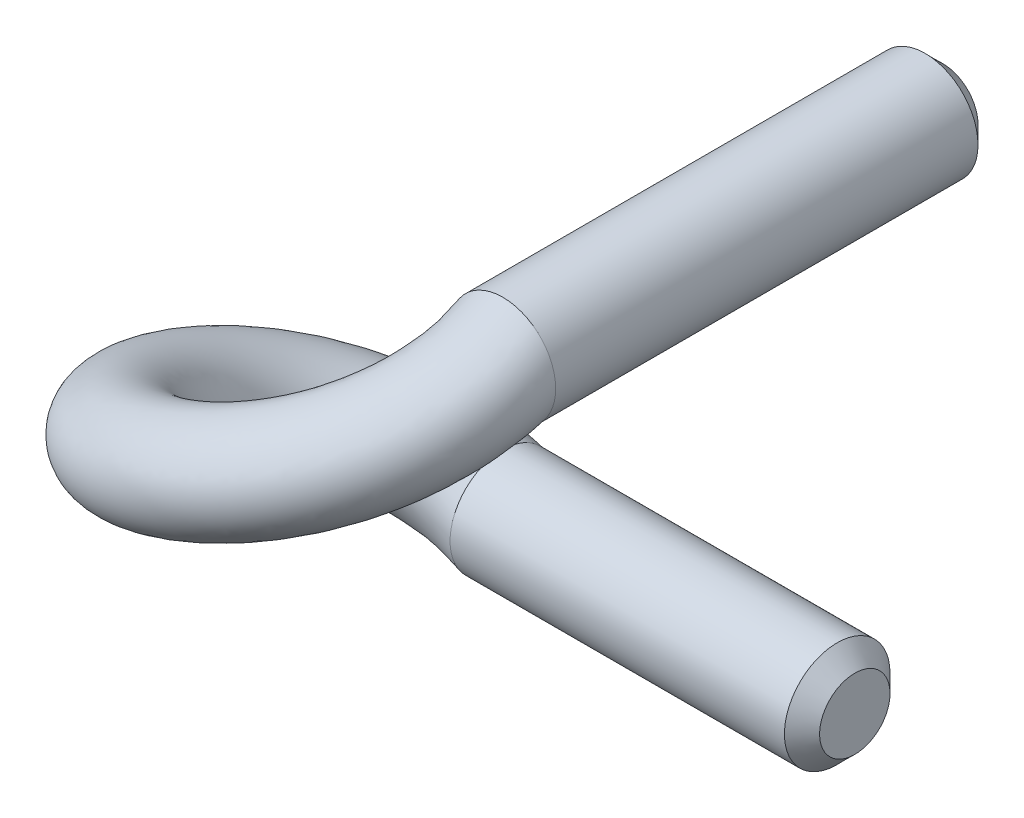
SolidWorks part; units mm, degrees
ref_plane "Ebene vorne" through (0, 0, 0) normal (0, 0, 1) x (1, 0, 0)
ref_plane "Ebene oben" through (0, 0, 0) normal (0, 1, 0) x (1, 0, 0)
ref_plane "Ebene rechts" through (0, 0, 0) normal (1, 0, 0) x (0, 0, -1)
sketch "Skizze1" plane through (0, 0, 0) normal (0, 0, 1) x (1, 0, 0)
  circle A0 centre (0, 0) radius 3
  dimension "D1" = 6
extrude "Aufsatz-Linear austragen1" add sketch "Skizze1" along normal blind 25
sketch "Skizze2" plane through (0, 0, 0) normal (0, 1, 0) x (1, 0, 0)
  line L0 (0, 0) -> (0, -25) construction
  line L1 (-3, -25) -> (3, -25) construction
  line L2 (-3, -25) -> (3, -25) construction
  circle A0 centre (-9, -25) radius 9
  dimension "D1" = 18
curve "Spirale/Helix1" pitch 22 height 16.5 turns 0.75
sketch "Skizze3" plane through (0, 0, 25) normal (0, 0, 1) x (1, 0, 0)
  circle A1 centre (0, 0) radius 3
  circle A2 centre (0, 0) radius 3
  dimension "D1" = 0
sweep "Austragung1" add profiles "Skizze3" path "Spirale/Helix1"
sketch "Skizze4" plane through (-9, 0, 0) normal (1, 0, 0) x (0, 0, -1)
  circle A1 centre (-16, -16.5) radius 3
  circle A2 centre (-16, -16.5) radius 3
  dimension "D1" = 0
extrude "Aufsatz-Linear austragen2" add sketch "Skizze4" along normal blind 20
chamfer "Fase1" distance 1 angle 45 2 edges at (11, -16.5, 13) (3, 0, 0)
